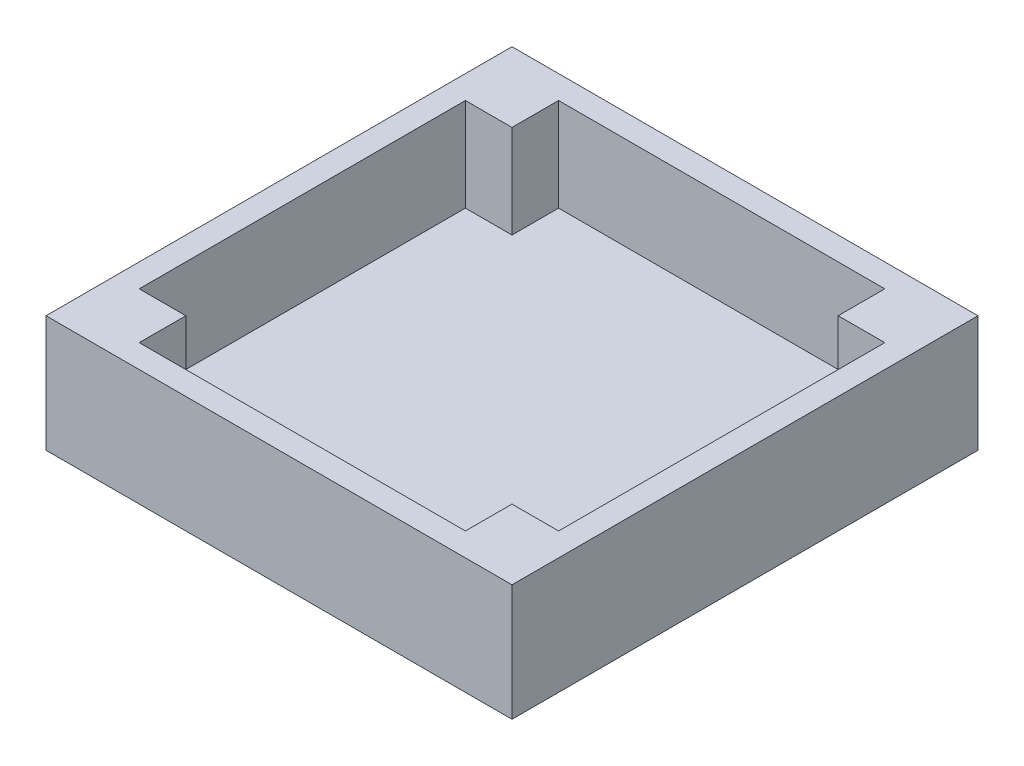
SolidWorks part; units mm, degrees
material "PC High Viscosity"
ref_plane "Front Plane" through (0, 0, 0) normal (0, 0, 1) x (1, 0, 0)
ref_plane "Top Plane" through (0, 0, 0) normal (0, 1, 0) x (1, 0, 0)
ref_plane "Right Plane" through (0, 0, 0) normal (1, 0, 0) x (0, 0, -1)
sketch "Sketch1" plane through (0, 0, 0) normal (0, 1, 0) x (1, 0, 0)
  line L1 (-30, -30) -> (30, -30)
  line L2 (-30, -30) -> (-30, 30)
  line L3 (-30, 30) -> (30, 30)
  line L4 (30, -30) -> (30, 30)
  line L5 (-30, -30) -> (30, 30) construction
  line L6 (-30, 30) -> (30, -30) construction
  point P0 (0, 0)
  dimension "D1" = 60
extrude "Boss-Extrude1" add sketch "Sketch1" along normal blind 15
shell "Shell1" thickness 3
sketch "Sketch2" plane through (0, 3, 0) normal (0, 1, 0) x (1, 0, 0)
  line L1 (-27, 27) -> (-21, 27)
  line L2 (-27, 27) -> (-27, 21)
  line L3 (-27, 21) -> (-21, 21)
  line L4 (-21, 27) -> (-21, 21)
  dimension "D1" = 6
extrude "Boss-Extrude2" add sketch "Sketch2" along normal up to surface (12 mm away) up to face at (0, 15, 0)
pattern_linear "LPattern1" count 2 spacing 48 along (1, 0, 0) count 2 spacing 48 along (0, 0, 1) of "Boss-Extrude2"
